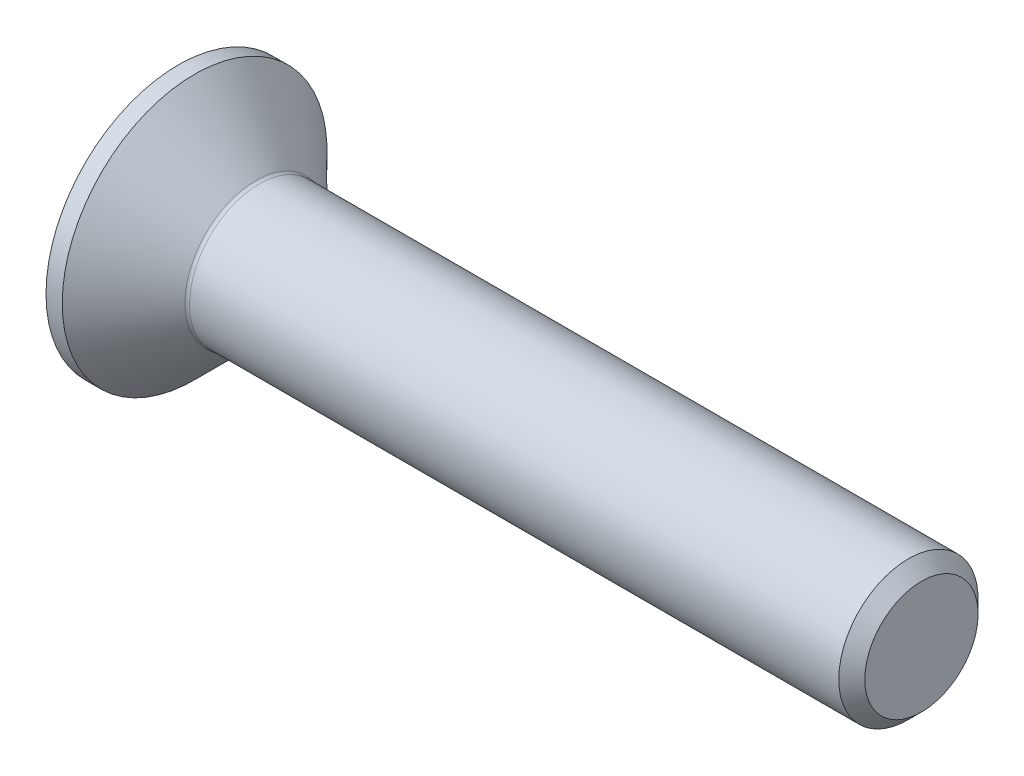
SolidWorks part; units mm, degrees
ref_plane "Plane1" through (0, 0, 0) normal (0, 0, 1) x (1, 0, 0)
ref_plane "Plane2" through (0, 0, 0) normal (0, 1, 0) x (1, 0, 0)
ref_plane "Plane3" through (0, 0, 0) normal (1, 0, 0) x (0, 0, -1)
sketch "BodySke" plane through (0, 0, 0) normal (0, 0, 1) x (1, 0, 0)
  line L0 (0, 0) -> (0, 2.85)
  line L1 (0.35, 2.85) -> (1.7, 1.5)
  line L2 (0, 2.85) -> (0.35, 2.85)
  line L3 (1.7, 1.5) -> (15.7195, 1.5)
  line L4 (16, 1.2195) -> (16, 0)
  line L5 (16, 0) -> (0, 0)
  line L6 (0, 0) -> (127, 0) construction
  line L7 (0.35, -2.85) -> (1.7, -1.5) construction
  line L8 (16, 1.2195) -> (15.7195, 1.5)
  line L9 (0, -2.85) -> (0.35, -2.85) construction
  line L10 (16, -1.2195) -> (15.7195, -1.5) construction
  line L11 (2.2, 7.85) -> (2.2, -14.375) construction
  line L12 (3.2, 16.35) -> (3.2, -5.875) construction
  dimension "Diameter" = 3
  dimension "Head_ht" = 1.7
  dimension "Length" = 16
  dimension "Body_ch_ang" = 45
  dimension "Head_dia" = 5.7
  dimension "Minor_dia" = 2.439
  dimension "Head_ang" = 90
  dimension "Advance" = 0.5
  dimension "Thread_nom" = 12.8
revolve "BaseBody" add sketch "BodySke" angle 360 about L6
cosmetic thread "ThreadCosmetic" parameters "Thread_length"=12.8, "Thread_minor"=2.439
fillet "Fillet1" radius 0.1 1 edges at (1.7, 0, 1.5)
sketch "Sketch2" plane through (0, 0, 0) normal (0, 0, 1) x (1, 0, 0)
  line L0 (0, 1.01) -> (1.2, 1.01)
  line L1 (1.2, 1.01) -> (1.7831, 0)
  line L2 (0, 0) -> (127, 0) construction
  line L3 (1.7831, 0) -> (0, 0)
  line L4 (0, 0) -> (0, 1.01)
  line L5 (0, -1.01) -> (1.2, -1.01) construction
  line L6 (0, 0) -> (47.625, 0) construction
  line L8 (0, 2.85) -> (0, -2.85) construction
  dimension "D2" = 60
  dimension "PreBroach_depth" = 1.2
  dimension "PreBroach_dia" = 2.02
revolve "PreBroach" cut sketch "Sketch2" angle 360 about L6
sketch "Sketch3" plane through (0, 0, 0) normal (-1, 0, 0) x (0, 0, 1)
  line L0 (-1.01, -0.5831) -> (-1.01, 0.5831)
  line L1 (-1.01, 0.5831) -> (0, 1.1662)
  line L2 (0, 1.1662) -> (1.01, 0.5831)
  line L3 (1.01, 0.5831) -> (1.01, -0.5831)
  line L4 (1.01, -0.5831) -> (0, -1.1662)
  line L5 (0, -1.1662) -> (-1.01, -0.5831)
  dimension "D1" = 1.01
  dimension "D2" = 1.01
  dimension "D3" = 2.02
  dimension "Hex_size" = 2.02
extrude "Hex" cut sketch "Sketch3" against normal blind 1.2
sketch "ThdSchSke" plane through (0, 0, 0) normal (0, 0, 1) x (1, 0, 0)
  line L0 (3.2, -1.2195) -> (3.0036, -1.5)
  line L1 (3.2, -1.2195) -> (3.3964, -1.5)
  line L2 (3.3964, -1.5) -> (3.3964, -1.875)
  line L3 (-3.175, 0) -> (5.1513, 0) construction
  line L4 (0, 2.85) -> (0, -2.85) construction
  line L5 (3.3964, -1.875) -> (3.0036, -1.875)
  line L6 (3.0036, -1.875) -> (3.0036, -1.5)
  dimension "Thread_minor" = 2.439
  dimension "Diameter" = 3
  dimension "Start" = 3.2
  dimension "SideAngle" = 55
  dimension "VeeAngle" = 70
  dimension "Overcut" = 3.75
revolve "ThreadSchematic" [suppressed] cut sketch "ThdSchSke" angle 360 about L3
pattern_linear "ThdSchPat" [suppressed]
equation "\"Thread_minor@ThreadCosmetic\"  =  \"Minor_dia@BodySke\""
equation "\"D1@Sketch3\" = \"Hex_size@Sketch3\" / 2"
equation "\"D2@Sketch3\" = \"D1@Sketch3\""
equation "\"D3@Sketch3\" = \"Hex_size@Sketch3\""
equation "\"Thread_length@ThreadCosmetic\" = ((sgn( (\"Length@BodySke\" - \"Advance@BodySke\" * 1.5 - \"Head_ht@BodySke\" ) - \"Thread_nom@BodySke\" )-1)*( (\"Length@BodySke\" - \"Advance@BodySke\" * 1.5 - \"Head_ht@BodySke\" ) - \"Thread_nom@BodySke\" ))/-2+ \"Thread_nom@BodySke\""
equation "\"Thread_minor@ThdSchSke\" = \"Minor_dia@BodySke\""
equation "\"Diameter@ThdSchSke\" = \"Diameter@BodySke\""
equation "\"Overcut@ThdSchSke\" = \"Diameter@BodySke\" * 1.25"
equation "\"Start@ThdSchSke\" = 0.000001 + \"Length@BodySke\" - \"Thread_length@ThreadCosmetic\"  '---Countersunk---"
equation "\"Num_threads@ThdSchPat\" = int( \"Thread_length@ThreadCosmetic\" / \"Advance@BodySke\" + 0.999 )  + 1"
equation "\"Advance@ThdSchPat\" = \"Thread_length@ThreadCosmetic\" /  (\"Num_threads@ThdSchPat\" - 1) 'relax it"
equation "\"Num_threads@ThdSchPat\" = \"Num_threads@ThdSchPat\" - sgn( \"Num_threads@ThdSchPat\" - 1) '---chamfered tips only---"
